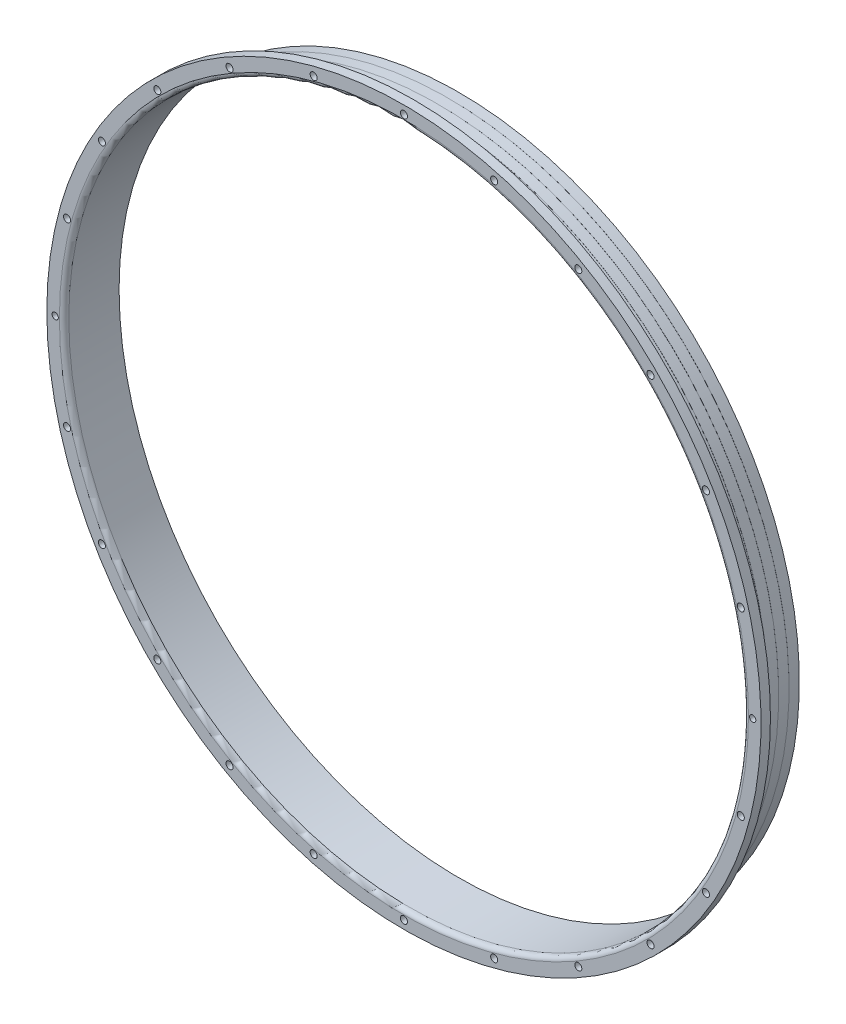
SolidWorks part; units mm, degrees
material "Isotropic CFRP"
ref_plane "Front Plane" through (0, 0, 0) normal (0, 0, 1) x (1, 0, 0)
ref_plane "Top Plane" through (0, 0, 0) normal (0, 1, 0) x (1, 0, 0)
ref_plane "Right Plane" through (0, 0, 0) normal (1, 0, 0) x (0, 0, -1)
sketch "Sketch1" plane through (0, 0, 0) normal (0, 0, 1) x (1, 0, 0)
  circle A0 centre (0, 0) radius 216.325
  dimension "D1" = 432.65
sketch "Sketch2" plane through (0, 0, 0) normal (1, 0, 0) x (0, 0, -1)
  line L0 (0, 227.325) -> (0, 219.325)
  line L1 (0, 216.325) -> (0, -216.325) construction
  line L2 (3, 216.325) -> (35, 216.325)
  line L3 (35, 216.325) -> (35, 217.39)
  line L4 (35, 217.39) -> (3.1, 217.39)
  line L5 (1.1, 219.39) -> (1.1, 227.325)
  line L6 (1.1, 227.325) -> (0, 227.325)
  arc A0 (3, 216.325) -> (0, 219.325) centre (3, 219.325) cw
  arc A1 (3.1, 217.39) -> (1.1, 219.39) centre (3.1, 219.39) cw
  point P12 (0, 216.325)
  dimension "D5" = 3
  dimension "D6" = 2
  dimension "D1" = 1.1
  dimension "D2" = 1.065
  dimension "D3" = 11
  dimension "D4" = 35
sweep "Sweep1" add profiles "Sketch2" path "Sketch1"
sketch "Sketch7" plane through (0, 0, 0) normal (1, 0, 0) x (0, 0, -1)
  line L4 (35, 216.325) -> (3, 216.325) construction
  line L5 (0, 227.325) -> (0, -227.325) construction
  line L10 (6, 216.325) -> (3, 216.325)
  line L12 (0, 227.325) -> (0, 219.325)
  line L13 (0, 227.325) -> (6, 227.325)
  line L14 (6, 227.325) -> (6, 216.325)
  line L17 (0, 0) -> (199.3317, 0) construction
  arc A2 (0, 219.325) -> (3, 216.325) centre (3, 219.325) ccw construction
  arc A4 (0, 219.325) -> (3, 216.325) centre (3, 219.325) ccw
  dimension "D1" = 6
revolve "Revolve3" add sketch "Sketch7" angle 360 about L17
fillet "Fillet1" radius 2 1 edges at (217.39, 0, -6)
sketch "Sketch8" plane through (0, 0, 0) normal (1, 0, 0) x (0, 0, -1)
  line L0 (35, 216.751) -> (28.4098, 216.751)
  line L1 (35, -217.39) -> (35, 217.39) construction
  line L2 (28.4098, 216.751) -> (28.1968, 216.964)
  line L3 (28.1968, 216.964) -> (21.6065, 216.964)
  line L4 (14.5903, 217.39) -> (35, 217.39)
  line L5 (21.6065, 216.964) -> (21.3935, 217.177)
  line L6 (21.3935, 217.177) -> (14.8033, 217.177)
  line L7 (14.8033, 217.177) -> (14.5903, 217.39)
  line L8 (14.5903, 217.39) -> (8, 217.39) construction
  line L9 (14.5903, 217.39) -> (14.5903, 217.177) construction
  line L10 (14.5903, 217.177) -> (14.8033, 217.177) construction
  line L11 (21.3935, 217.177) -> (21.3935, 216.964) construction
  line L12 (21.3935, 216.964) -> (21.6065, 216.964) construction
  line L13 (28.1968, 216.964) -> (28.1968, 216.751) construction
  line L14 (28.1968, 216.751) -> (28.4098, 216.751) construction
  line L16 (35, 217.39) -> (35, 216.751)
  dimension "D1" = 0.213
revolve "Cut-Revolve1" cut sketch "Sketch8" angle 360 about axis through (0, 0, -21) along (0, 0, 1)
hole_wizard "M4 Clearance Hole1" positions "Sketch4" profile "Sketch5" hole size "M4" standard "Ansi Metric" end condition through all
sketch "Sketch4" plane through (0, 0, 0) normal (0, 0, 1) x (1, 0, 0)
  line L0 (0, 222) -> (0, 0) construction
  point P0 (0, 222)
  dimension "D1" = 222
sketch "Sketch5" plane through (0, 222, 0) normal (1, 0, 0) x (0, -1, 0)
  line L0 (0, 0) -> (0, 35)
  line L1 (0, 35) -> (2.25, 35)
  line L2 (2.25, 35) -> (2.25, 0)
  line L5 (2.25, 0) -> (0, 0)
  line L11 (0, -6.35) -> (0, 107.95) construction
  dimension "Thru Hole Dia." = 4.5
  dimension "Thru Hole Depth" = 35
ref_axis "Axis1" through (0, 0, -21) along (0, 0, 1)
pattern_circular "CirPattern1" count 24 over 360 about axis through (0, 0, 0) along (0, 0, 1) of "M4 Clearance Hole1"
sketch "Sketch6" plane through (0, 0, 0) normal (0, 0, 1) x (1, 0, 0)
  circle A0 centre (-222, 0) radius 2.25 construction
  circle A1 centre (222, 0) radius 2.25 construction
  circle A2 centre (-222, 0) radius 2.25
  circle A3 centre (222, 0) radius 2.25
  circle A4 centre (222, 0) radius 2
  circle A5 centre (-222, 0) radius 2
  dimension "D1" = 4
extrude "Boss-Extrude1" add sketch "Sketch6" against normal up to surface (6 mm away) up to face at (59.7078, 214.4355, -6)
sketch "Sketch10" [suppressed] plane through (0, 0, 0) normal (1, 0, 0) x (0, 0, -1)
  line L0 (0, 227.325) -> (6, 227.325)
  line L1 (0, 227.325) -> (0, 232.325)
  line L2 (6, 227.325) -> (6, 232.325)
  line L3 (0, 232.325) -> (6, 232.325)
  line L4 (35, 216.751) -> (35, 216.325)
  line L5 (35, 216.751) -> (40, 216.751)
  line L6 (35, 216.325) -> (40, 216.325)
  line L7 (40, 216.751) -> (40, 216.325)
  dimension "D1" = 40
  dimension "D2" = 16
  dimension "D3" = 5
  dimension "D4" = 5
revolve "Revolve4" [suppressed] add sketch "Sketch10" angle 360 about axis through (0, 0, -21) along (0, 0, 1)
sketch "tapered layup sketch" [suppressed] plane through (0, 0, 0) normal (0, 1, 0) x (0, 0, -1)
  line L0 (21.1183, 216.964) -> (21.1183, 216.751)
  line L1 (27.9215, 216.751) -> (27.9215, 216.538)
  line L2 (14.315, 217.177) -> (14.315, 216.964)
  line L4 (8, 217.177) -> (3, 217.177)
  line L5 (0.852, 219.325) -> (0.852, 232.325)
  line L6 (40, 216.538) -> (40, 216.325)
  line L7 (40, -216.751) -> (40, 216.751) construction
  line L8 (5.787, 219.39) -> (5.787, 232.325)
  line L9 (6, 232.325) -> (0, 232.325) construction
  line L10 (14.715, 216.964) -> (3, 216.964)
  line L11 (0.639, 219.325) -> (0.639, 232.325)
  line L12 (21.5183, 216.751) -> (3, 216.751)
  line L13 (0.426, 219.325) -> (0.426, 232.325)
  line L14 (28.3215, 216.538) -> (3, 216.538)
  line L15 (28.3215, 216.538) -> (40, 216.538)
  line L16 (28.1085, 216.751) -> (28.3215, 216.538)
  line L17 (21.5183, 216.751) -> (28.1085, 216.751)
  line L18 (21.3053, 216.964) -> (21.5183, 216.751)
  line L19 (14.715, 216.964) -> (21.3053, 216.964)
  line L20 (14.502, 217.177) -> (14.715, 216.964)
  line L21 (8, 217.177) -> (14.502, 217.177)
  line L22 (28.3215, 216.538) -> (40, 216.538)
  line L23 (28.1085, 216.751) -> (28.3215, 216.538)
  line L24 (21.5183, 216.751) -> (28.1085, 216.751)
  line L25 (21.3053, 216.964) -> (21.5183, 216.751)
  line L26 (14.715, 216.964) -> (21.3053, 216.964)
  line L27 (14.502, 217.177) -> (14.715, 216.964)
  line L28 (8, 217.177) -> (14.502, 217.177)
  line L29 (0.213, 219.325) -> (0.213, 232.325)
  line L30 (40, 216.325) -> (3, 216.325)
  line L31 (0, 219.325) -> (0, 232.325)
  line L32 (0, 232.325) -> (0.213, 232.325)
  line L33 (0.213, 232.325) -> (0.426, 232.325)
  line L34 (0.426, 232.325) -> (0.639, 232.325)
  line L35 (0.639, 232.325) -> (0.852, 232.325)
  line L36 (0.852, 232.325) -> (5.787, 232.325)
  line L37 (5.787, 232.325) -> (6, 232.325)
  line L38 (6, 232.325) -> (6, 219.39)
  line L39 (6, -232.325) -> (6, 232.325) construction
  line L40 (8, -217.39) -> (14.5903, -217.39)
  line L41 (14.5903, 217.39) -> (8, 217.39)
  line L42 (14.5903, 217.39) -> (8, 217.39)
  line L43 (40, 216.751) -> (40, 216.538)
  line L44 (14.5903, 217.39) -> (14.8033, 217.177)
  line L45 (14.8033, -217.177) -> (14.5903, -217.39)
  line L47 (14.5903, 217.39) -> (14.8033, 217.177)
  line L48 (21.3935, -217.177) -> (14.8033, -217.177)
  line L49 (14.8033, 217.177) -> (21.3935, 217.177)
  line L50 (14.8033, 217.177) -> (21.3935, 217.177)
  line L52 (21.3935, 217.177) -> (21.6065, 216.964)
  line L53 (21.6065, -216.964) -> (21.3935, -217.177)
  line L55 (21.3935, 217.177) -> (21.6065, 216.964)
  line L56 (28.1968, -216.964) -> (21.6065, -216.964)
  line L57 (21.6065, 216.964) -> (28.1968, 216.964)
  line L58 (21.6065, 216.964) -> (28.1968, 216.964)
  line L60 (28.1968, 216.964) -> (28.4098, 216.751)
  line L61 (28.4098, -216.751) -> (28.1968, -216.964)
  line L63 (28.1968, 216.964) -> (28.4098, 216.751)
  line L64 (40, -216.751) -> (28.4098, -216.751)
  line L65 (28.4098, 216.751) -> (40, 216.751)
  line L66 (28.4098, 216.751) -> (40, 216.751)
  arc A0 (3, 217.177) -> (0.852, 219.325) centre (3, 219.325) cw
  arc A1 (0, 219.325) -> (3, 216.325) centre (3, 219.325) ccw
  arc A2 (6, 219.39) -> (8, 217.39) centre (8, 219.39) ccw
  arc A3 (3, 216.964) -> (0.639, 219.325) centre (3, 219.325) cw
  arc A4 (5.787, 219.39) -> (8, 217.177) centre (8, 219.39) ccw
  arc A5 (5.787, 219.39) -> (8, 217.177) centre (8, 219.39) ccw
  arc A6 (0, 219.325) -> (3, 216.325) centre (3, 219.325) ccw construction
  arc A7 (3, 216.751) -> (0.426, 219.325) centre (3, 219.325) cw
  arc A8 (3, 216.538) -> (0.213, 219.325) centre (3, 219.325) cw
  arc A9 (8, -217.39) -> (6, -219.39) centre (8, -219.39) ccw
  arc A11 (6, 219.39) -> (8, 217.39) centre (8, 219.39) ccw
  dimension "D2" = 0.4
  dimension "D3" = 0.4
  dimension "D4" = 0.4
  dimension "D1" = 0.213
